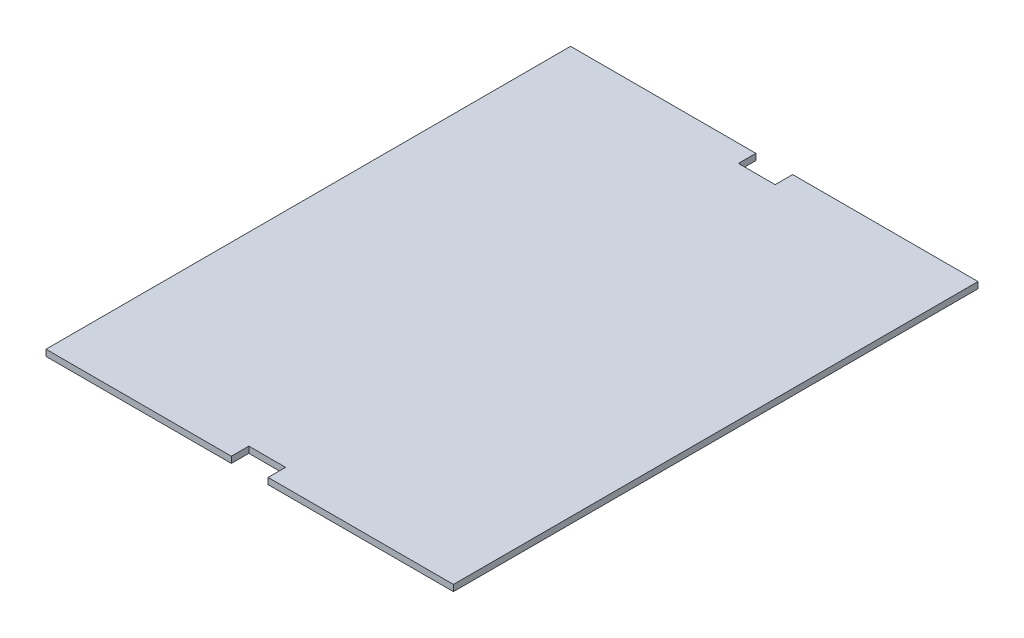
SolidWorks part; units mm, degrees
ref_plane "Alzado" through (0, 0, 0) normal (0, 0, 1) x (1, 0, 0)
ref_plane "Planta" through (0, 0, 0) normal (0, 1, 0) x (1, 0, 0)
ref_plane "Vista lateral" through (0, 0, 0) normal (1, 0, 0) x (0, 0, -1)
sketch "Croquis1" plane through (0, 0, 0) normal (0, 1, 0) x (1, 0, 0)
  line L1 (-58.25, -75) -> (58.25, -75)
  line L2 (-58.25, -75) -> (-58.25, 75)
  line L3 (-58.25, 75) -> (58.25, 75)
  line L4 (58.25, -75) -> (58.25, 75)
  line L5 (-58.25, -75) -> (58.25, 75) construction
  line L6 (-58.25, 75) -> (58.25, -75) construction
  point P0 (0, 0)
  dimension "D1" = 116.5
  dimension "D2" = 150
extrude "Saliente-Extruir1" add sketch "Croquis1" along normal blind 1.8
sketch "Croquis2" plane through (0, 1.8, 0) normal (0, 1, 0) x (1, 0, 0)
  line L0 (-58.25, -75) -> (58.25, -75) construction
  line L1 (-5.25, -75) -> (5.25, -75)
  line L2 (-5.25, -75) -> (-5.25, -70)
  line L3 (-5.25, -70) -> (5.25, -70)
  line L4 (5.25, -75) -> (5.25, -70)
  line L5 (-58.25, 75) -> (-58.25, -75) construction
  line L6 (58.25, -75) -> (58.25, 75) construction
  line L7 (-0.99, 0) -> (0.99, 0) construction
  line L8 (-5.25, 75) -> (-5.25, 70)
  line L9 (5.25, 75) -> (5.25, 70)
  line L10 (-5.25, 75) -> (5.25, 75)
  line L11 (-5.25, 70) -> (5.25, 70)
  dimension "D1" = 5
  dimension "D2" = 53
  dimension "D3" = 53
extrude "Cortar-Extruir1" cut sketch "Croquis2" against normal through all
